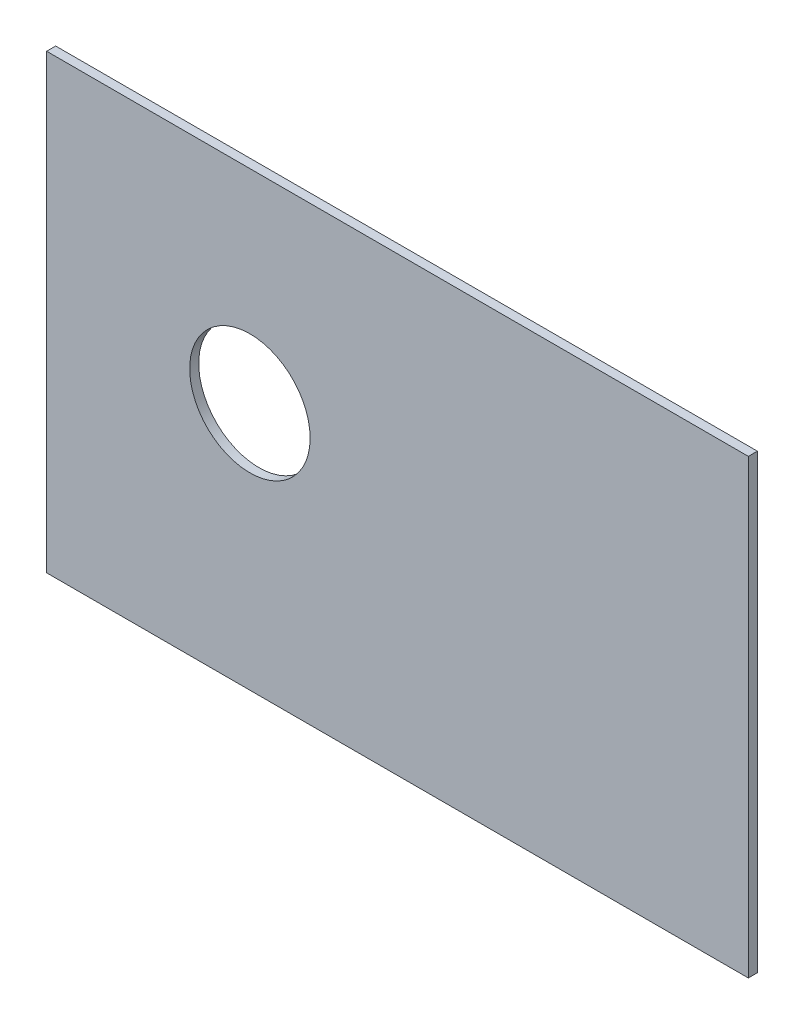
SolidWorks part; units mm, degrees
ref_plane "Front Plane" through (0, 0, 0) normal (0, 0, 1) x (1, 0, 0)
ref_plane "Top Plane" through (0, 0, 0) normal (0, 1, 0) x (1, 0, 0)
ref_plane "Right Plane" through (0, 0, 0) normal (1, 0, 0) x (0, 0, -1)
sketch "Sketch1" plane through (0, 0, 0) normal (0, 0, 1) x (1, 0, 0)
  line L1 (72.9141, -76.938) -> (116.5, -76.938) construction
  line L4 (58.0433, 30.3517) -> (114.1466, -76.938) construction
  line L7 (55.3848, 28.9615) -> (110.7612, -76.938) construction
  line L8 (-58.0433, -30.3517) -> (14.8708, -169.7896) construction
  line L9 (-55.3848, -28.9615) -> (17.5292, -168.3995) construction
  line L42 (42.5, 40) -> (77.5, 40) construction
  line L43 (42.5, 40) -> (42.5, -41) construction
  line L46 (116.5, -73.938) -> (72.9141, -73.938) construction
  line L47 (116.5, -204.938) -> (72.9141, -204.938) construction
  line L48 (42.5, -41) -> (77.5, -41) construction
  line L49 (77.5, 40) -> (77.5, -41) construction
  line L50 (39.5, 84) -> (103.5, 84) construction
  line L51 (49.5, 121.8401) -> (49.5, 40) construction
  line L52 (87.5, 121.8401) -> (87.5, 40) construction
  line L55 (0, 100) -> (0, -46) construction
  line L56 (-9.5, 17) -> (-9.5, -4.7961) construction
  line L57 (-39.5, -17) -> (9.7212, -17) construction
  line L58 (-39.5, 17) -> (-5.59, 17) construction
  line L63 (103.5, 84) -> (103.5, -41) construction
  line L64 (39.5, 84) -> (39.5, -41) construction
  line L65 (39.5, 17) -> (5.59, 17) construction
  line L66 (39.5, -17) -> (-9.7212, -17) construction
  line L67 (9.5, 17) -> (9.5, -4.7961) construction
  line L68 (-39.5, 84) -> (-39.5, -41) construction
  line L69 (-103.5, 84) -> (-103.5, -41) construction
  line L70 (-87.5, 121.8401) -> (-87.5, 40) construction
  line L71 (-49.5, 121.8401) -> (-49.5, 40) construction
  line L72 (-39.5, 84) -> (-103.5, 84) construction
  line L73 (-77.5, 40) -> (-77.5, -41) construction
  line L74 (-42.5, -41) -> (-77.5, -41) construction
  line L75 (-42.5, 40) -> (-42.5, -41) construction
  line L76 (-42.5, 40) -> (-77.5, 40) construction
  line L77 (-20.5, 80) -> (20.5, 80) construction
  line L78 (-116.5, 104) -> (116.5, 104)
  line L79 (-116.5, 104) -> (-116.5, -46)
  line L80 (-116.5, -46) -> (116.5, -46)
  line L81 (116.5, 104) -> (116.5, -46)
  line L82 (72.9141, -201.938) -> (116.5, -201.938) construction
  line L83 (-65.5, -62.5) -> (65.5, -62.5) construction
  line L84 (-65.5, 0) -> (-65.5, -46) construction
  line L85 (65.5, 0) -> (65.5, -46) construction
  line L86 (-60, 40) -> (-60, -41) construction
  line L87 (60, 40) -> (60, -41) construction
  line L91 (116.5, -81.4386) -> (136.4983, -119.6826) construction
  line L92 (128.2989, -110.4765) -> (132.6262, -118.7518) construction
  circle A3 centre (0, 0) radius 62.5 construction
  circle A4 centre (49.5, 84) radius 2 construction
  circle A8 centre (87.5, 84) radius 2 construction
  circle A9 centre (49.5, 53) radius 2 construction
  circle A10 centre (87.5, 53) radius 2 construction
  circle A15 centre (103.5, 24) radius 3 construction
  circle A16 centre (103.5, -27) radius 3 construction
  circle A17 centre (39.5, 17) radius 2 construction
  circle A18 centre (39.5, -17) radius 2 construction
  circle A19 centre (9.5, 17) radius 2 construction
  circle A20 centre (9.5, -17) radius 2 construction
  circle A21 centre (20.5, 80) radius 2 construction
  circle A22 centre (-20.5, 80) radius 2 construction
  circle A23 centre (-9.5, -17) radius 2 construction
  circle A24 centre (-9.5, 17) radius 2 construction
  circle A25 centre (-39.5, -17) radius 2 construction
  circle A26 centre (-39.5, 17) radius 2 construction
  circle A27 centre (-103.5, -27) radius 3 construction
  circle A28 centre (-103.5, 24) radius 3 construction
  circle A29 centre (-87.5, 53) radius 2 construction
  circle A30 centre (-49.5, 53) radius 2 construction
  circle A31 centre (-87.5, 84) radius 2 construction
  circle A32 centre (-49.5, 84) radius 2 construction
  circle A33 centre (0, 80) radius 13 construction
  circle A34 centre (0, 100) radius 2 construction
  circle A35 centre (0, 0) radius 3 construction
  arc A37 (72.9141, -76.938) -> (72.9141, -201.938) centre (72.9141, -139.438) ccw construction
  circle A38 centre (0, 0) radius 65.5 construction
  arc A39 (72.9141, -204.938) -> (72.9141, -73.938) centre (72.9141, -139.438) cw construction
  circle A40 centre (72.9141, -139.438) radius 62.5 construction
  dimension "D8" = 35
  dimension "D23" = 4
  dimension "D11" = 4
  dimension "D12" = 4
  dimension "D13" = 4
  dimension "D14" = 4
  dimension "D10" = 6
  dimension "D19" = 6
  dimension "D25" = 4
  dimension "D29" = 4
  dimension "D30" = 4
  dimension "D32" = 4
  dimension "D38" = 26
  dimension "D39" = 4
  dimension "D42" = 6
  dimension "D45" = 3
  dimension "D6" = 62.5
  dimension "D7" = 125
  dimension "D24" = 3
  dimension "D4" = 13
  dimension "D5" = 125
  dimension "D9" = 81
  dimension "D15" = 31
  dimension "D16" = 13
  dimension "D17" = 7
  dimension "D18" = 38
  dimension "D20" = 26
  dimension "D21" = 16
  dimension "D22" = 51
  dimension "D26" = 3
  dimension "D27" = 23
  dimension "D28" = 34
  dimension "D31" = 30
  dimension "D33" = 22
  dimension "D34" = 40
  dimension "D35" = 42.5
  dimension "D36" = 13
  dimension "D37" = 13
  dimension "D40" = 20
  dimension "D41" = 17
  dimension "D43" = 4
  dimension "D44" = 150
  dimension "D46" = 3
  dimension "D47" = 3
  dimension "D48" = 3
extrude "Boss-Extrude1" add sketch "Sketch1" along normal blind 3 contours A37 L1 L80 L81 L78 L79 L82 A35 A34 A33 A31 A29 A27 A25 A23 L42 L49 L48 L43 L76 L75 L74 L73 A4 A8 A9 A10 A15 A16 A17 A18
sketch "Sketch2" plane through (0, 0, 3) normal (0, 0, 1) x (1, 0, 0)
  circle A0 centre (-49, 36.5) radius 20
  circle A2 centre (-49, 36.5) radius 62.5 construction
  dimension "D1" = 40
extrude "Cut-Extrude3" cut sketch "Sketch2" against normal through all
